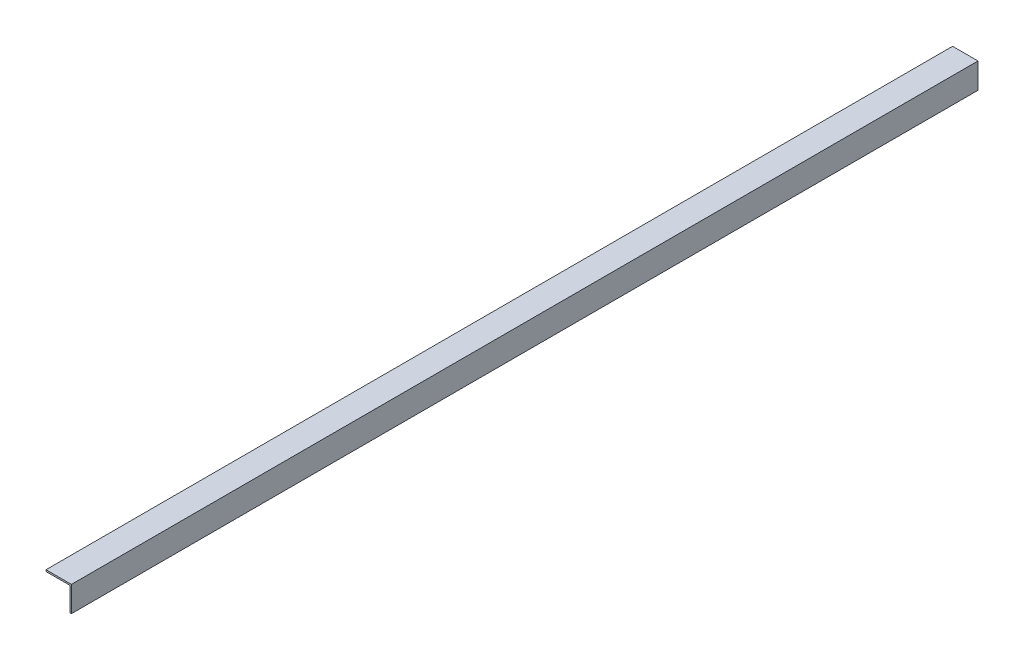
SolidWorks part; units mm, degrees
material "6063-T6"
ref_plane "Front Plane" through (0, 0, 0) normal (0, 0, 1) x (1, 0, 0)
ref_plane "Top Plane" through (0, 0, 0) normal (0, 1, 0) x (1, 0, 0)
ref_plane "Right Plane" through (0, 0, 0) normal (1, 0, 0) x (0, 0, -1)
sketch "Sketch1" plane through (0, 0, 0) normal (0, 0, 1) x (1, 0, 0)
  line L0 (0, 0) -> (-50.8, 0)
  line L1 (-50.8, 0) -> (-50.8, -3.175)
  line L2 (-50.8, -3.175) -> (-3.175, -3.175)
  line L3 (-3.175, -3.175) -> (-3.175, -50.8)
  line L4 (-3.175, -50.8) -> (0, -50.8)
  line L5 (0, -50.8) -> (0, 0)
  dimension "D1" = 50.8
  dimension "D2" = 3.175
extrude "Boss-Extrude1" add sketch "Sketch1" along normal blind 1812.925
sketch "Sketch2" plane through (0, 0, 0) normal (0, 1, 0) x (1, 0, 0)
  line L0 (0, 0) -> (-50.8, 0) construction
  line L1 (0, -1812.925) -> (0, 0) construction
  circle A0 centre (-38.1, -37.3063) radius 10.3188
  circle A1 centre (-38.1, -1775.6188) radius 10.3187
  circle A2 centre (-33.3375, -93.6625) radius 7.1438
  circle A3 centre (-33.3375, -449.2625) radius 7.1438
  circle A4 centre (-33.3375, -855.6625) radius 7.1437
  circle A5 centre (-33.3375, -1262.0625) radius 7.1438
  circle A6 centre (-33.3375, -1719.2625) radius 7.1438
  dimension "D1" = 20.6375
  dimension "D2" = 14.2875
  dimension "D3" = 37.3062
  dimension "D4" = 38.1
  dimension "D5" = 1775.6188
  dimension "D6" = 33.3375
  dimension "D7" = 93.6625
  dimension "D8" = 449.2625
  dimension "D9" = 855.6625
  dimension "D10" = 1262.0625
  dimension "D11" = 1719.2625
extrude "Cut-Extrude1" [suppressed] cut sketch "Sketch2" against normal through all
extrude "Cut-Extrude3" [suppressed] cut sketch "Sketch4" against normal blind 44.45
sketch "Sketch4" plane through (-2.0299, 0, 893.1633) normal (0, 1, 0) x (1, 0, 0)
  circle A0 centre (-36.0701, 697.9008) radius 3.9687
pattern_linear "LPattern1" [suppressed] count 15 spacing 101.6
